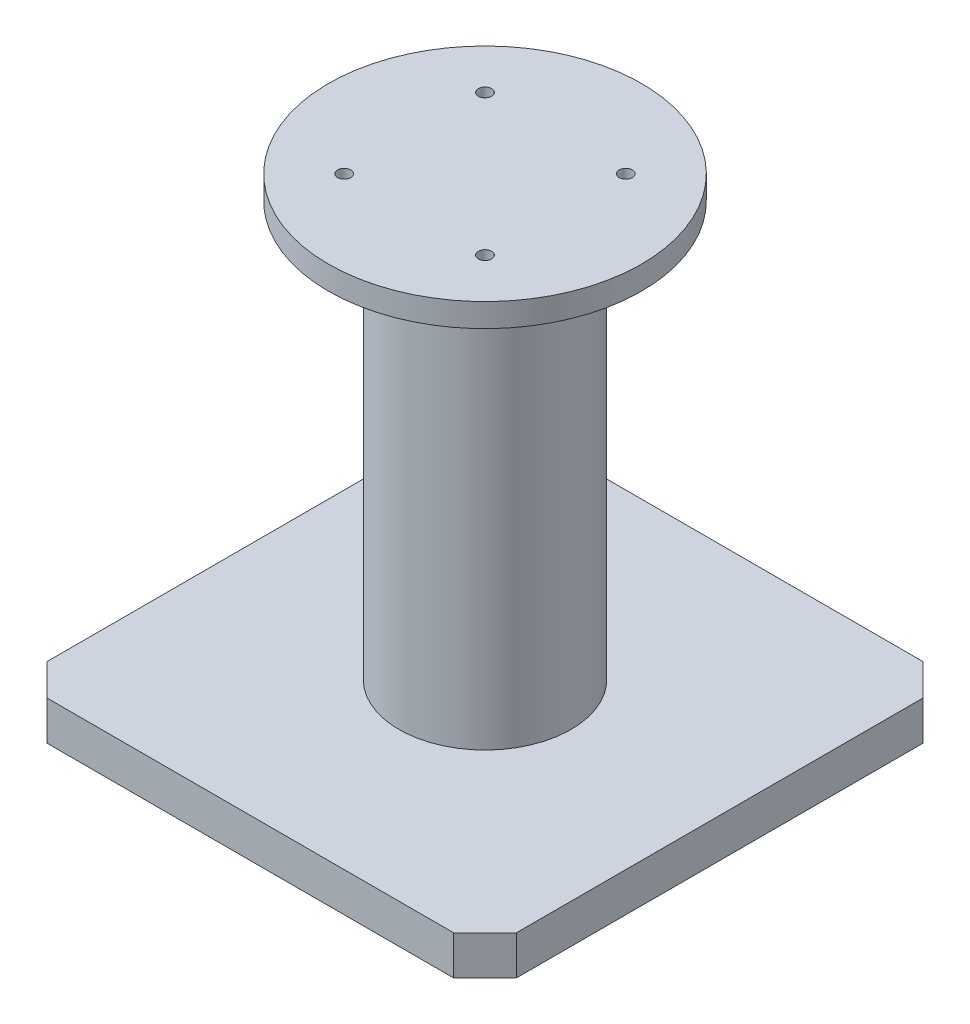
SolidWorks part; units mm, degrees
ref_plane "Front Plane" through (0, 0, 0) normal (0, 0, 1) x (1, 0, 0)
ref_plane "Top Plane" through (0, 0, 0) normal (0, 1, 0) x (1, 0, 0)
ref_plane "Right Plane" through (0, 0, 0) normal (1, 0, 0) x (0, 0, -1)
sketch "Sketch1" plane through (0, 0, 0) normal (0, 1, 0) x (1, 0, 0)
  circle A0 centre (0, 0) radius 100
  dimension "D1" = 200
extrude "Boss-Extrude1" add sketch "Sketch1" against normal blind 15
sketch "Sketch2" plane through (0, -15, 0) normal (0, -1, 0) x (1, 0, 0)
  circle A0 centre (0, 0) radius 55
  dimension "D1" = 110
extrude "Boss-Extrude2" add sketch "Sketch2" along normal blind 265
sketch "Sketch3" plane through (0, -280, 0) normal (0, -1, 0) x (1, 0, 0)
  line L0 (-150, 130) -> (-130, 150)
  line L1 (-130, -150) -> (130, -150)
  line L2 (-150, -130) -> (-150, 130)
  line L3 (-130, 150) -> (130, 150)
  line L4 (150, -130) -> (150, 130)
  line L5 (0, 150) -> (0, -150) construction
  line L6 (-150, 0) -> (150, 0) construction
  line L7 (-130, -150) -> (-150, -130)
  line L8 (130, -150) -> (150, -130)
  line L9 (150, 130) -> (130, 150)
  point P0 (0, 0)
  point P1 (150, 150)
  point P2 (-150, -150)
  point P3 (-150, 150)
  point P192 (150, -150)
  dimension "D1" = 300
  dimension "D2" = 300
  dimension "D3" = 150
  dimension "D4" = 150
extrude "Boss-Extrude3" add sketch "Sketch3" along normal blind 25
sketch "Sketch4" plane through (0, 0, 0) normal (0, 1, 0) x (1, 0, 0)
  line L0 (0, 0) -> (0, 63.6396) construction
  line L1 (0, 0) -> (-63.6396, 0) construction
  circle A0 centre (0, 0) radius 63.6396
  circle A1 centre (-45, 45) radius 4.25
  circle A2 centre (45, 45) radius 4.25
  circle A3 centre (45, -45) radius 4.25
  circle A4 centre (-45, -45) radius 4.25
  dimension "D1" = 8.5
  dimension "D2" = 45
  dimension "D3" = 45
extrude "Cut-Extrude1" cut sketch "Sketch4" against normal blind 25 contours A1 | A2 | A4 | A3
